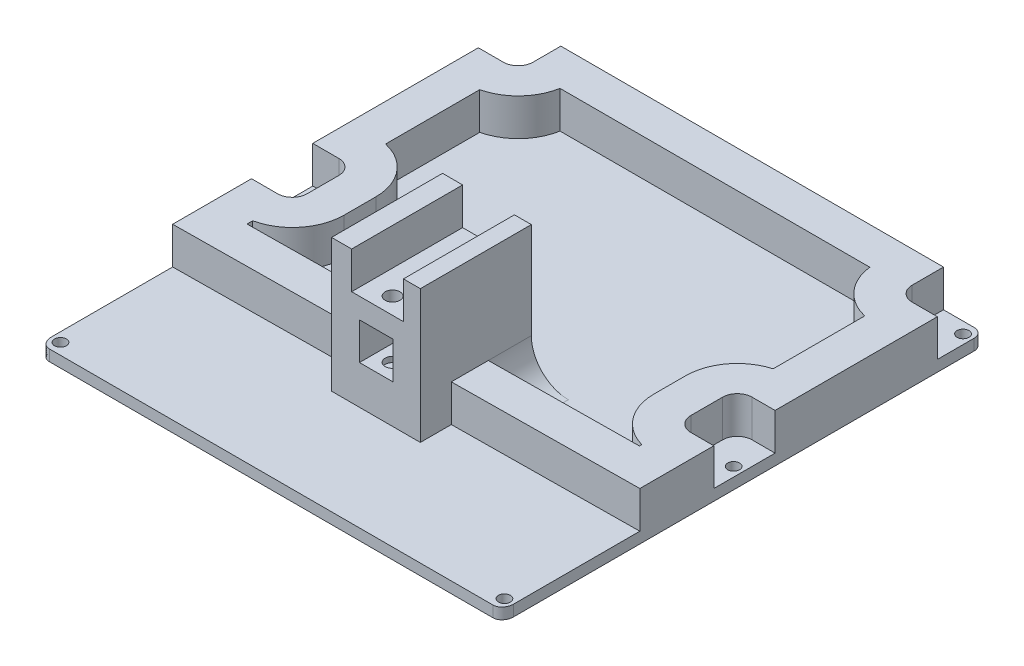
SolidWorks part; units mm, degrees
ref_plane "Front Plane" through (0, 0, 0) normal (0, 0, 1) x (1, 0, 0)
ref_plane "Top Plane" through (0, 0, 0) normal (0, 1, 0) x (1, 0, 0)
ref_plane "Right Plane" through (0, 0, 0) normal (1, 0, 0) x (0, 0, -1)
sketch "Sketch1" plane through (0, 0, 0) normal (0, 1, 0) x (-1, 0, 0)
  line L12 (60, 65) -> (-60, 65)
  line L13 (-62.5, 61.9766) -> (-62.5, -62.5)
  line L14 (-60, -65) -> (60, -65)
  line L15 (62.5, -62.5) -> (62.5, 61.9766)
  circle A3 centre (60, 61.9766) radius 1.6
  arc A6 (-62.5, -62.5) -> (-60, -65) centre (-60, -62.5) ccw
  arc A7 (60, -65) -> (62.5, -62.5) centre (60, -62.5) ccw
  circle A9 centre (-60, 61.9766) radius 1.6
  circle A11 centre (-60, 0.0234) radius 1.6
  circle A13 centre (60, 0.0234) radius 1.6
  circle A15 centre (-60, -61.9766) radius 1.6
  circle A17 centre (60, -61.9766) radius 1.6
  spline S2 degree 3 poles (-60, 65) (-60.1828, 65) (-60.3613, 64.9755) (-60.7103, 64.8812) (-60.8803, 64.8107) (-61.1953, 64.6346) (-61.3442, 64.527) (-61.614, 64.2859) (-61.7356, 64.1524) (-62.0644, 63.7166) (-62.2274, 63.3897) (-62.4459, 62.6988) (-62.5, 62.3406) (-62.5, 61.9766) knots 0 0 0 0 0.125 0.125 0.25 0.25 0.375 0.375 0.5 0.5 0.75 0.75 1 1 1 1
  spline S3 degree 3 poles (62.5, 61.9766) (62.5, 62.3418) (62.4462, 62.6962) (62.2839, 63.2118) (62.215, 63.3825) (62.0516, 63.705) (61.9573, 63.8579) (61.7414, 64.1454) (61.6183, 64.2815) (61.3473, 64.5247) (61.2009, 64.631) (60.8836, 64.8094) (60.7133, 64.8801) (60.3654, 64.9748) (60.1838, 65) (60, 65) knots 0 0 0 0 0.25 0.25 0.375 0.375 0.5 0.5 0.625 0.625 0.75 0.75 0.875 0.875 1 1 1 1
extrude "Boss-Extrude1" add sketch "Sketch1" along normal blind 3
sketch "Sketch2" plane through (0, 3, 0) normal (0, 1, 0) x (1, 0, 0)
  line L0 (-62.5, -29.1617) -> (62.5, -27.8758)
  line L1 (-62.5, 53.4681) -> (-55.7296, 53.4681)
  line L2 (-62.5, -7.8419) -> (-55.4569, -7.8419)
  line L4 (-60, -65) -> (60, -65)
  line L5 (62.5, -61.9766) -> (62.5, 62.5)
  line L6 (60, 65) -> (-60, 65)
  line L7 (-62.5, 62.5) -> (-62.5, -61.9766)
  line L9 (62.5, -27.8758) -> (62.5, -7.8748)
  line L10 (51.7018, 65) -> (-51.7296, 65)
  line L11 (-62.5, 53.4681) -> (-62.5, 8.71)
  line L12 (-62.5, 8.71) -> (-55.4569, 8.71)
  line L13 (-51.4569, -3.8419) -> (-51.4569, 4.71)
  line L16 (-51.7296, 57.4681) -> (-51.7296, 65)
  line L17 (56.2971, -7.8748) -> (62.5, -7.8748)
  line L18 (52.2971, -3.8748) -> (52.2971, 4.6771)
  line L19 (56.2971, 8.6771) -> (62.5, 8.6771)
  line L21 (55.7018, 52.5438) -> (62.5, 52.5438)
  line L22 (51.7018, 56.5438) -> (51.7018, 65)
  line L25 (62.5, 8.6771) -> (62.5, 52.5438)
  line L26 (-62.5, -7.8419) -> (-62.5, -29.1617)
  line L27 (-52.5, -19.0583) -> (52.5, -17.9781)
  line L28 (52.5, -17.9781) -> (52.5, -17.35)
  line L29 (52.5, -17.35) -> (52.5, -17.35)
  line L30 (42.2971, -3.8748) -> (42.2971, 4.6771)
  line L31 (52.5, 18.1523) -> (52.5, 18.1523)
  line L32 (52.5, 18.1523) -> (52.5, 42.9149)
  line L33 (52.5, 42.9149) -> (52.5, 42.9149)
  line L34 (41.7872, 55) -> (41.7872, 55)
  line L35 (41.7872, 55) -> (-41.9488, 55)
  line L36 (-41.9488, 55) -> (-41.9488, 55)
  line L37 (-52.5, 43.8457) -> (-52.5, 43.8457)
  line L38 (-52.5, 43.8457) -> (-52.5, 18.3941)
  line L39 (-52.5, 18.3941) -> (-52.5, 18.3941)
  line L40 (-41.4569, -3.8419) -> (-41.4569, 4.71)
  line L41 (-52.5, -17.5261) -> (-52.5, -17.5261)
  line L42 (-52.5, -17.5261) -> (-52.5, -19.0583)
  arc A2 (62.5, 62.5) -> (60, 65) centre (60, 62.5) ccw
  arc A3 (-60, 65) -> (-62.5, 62.5) centre (-60, 62.5) ccw
  arc A12 (51.7018, 56.5438) -> (55.7018, 52.5438) centre (55.7018, 56.5438) ccw
  arc A13 (52.2971, 4.6771) -> (56.2971, 8.6771) centre (56.2971, 4.6771) cw
  arc A14 (52.2971, -3.8748) -> (56.2971, -7.8748) centre (56.2971, -3.8748) ccw
  arc A15 (-51.7296, 57.4681) -> (-55.7296, 53.4681) centre (-55.7296, 57.4681) cw
  arc A16 (-55.4569, 8.71) -> (-51.4569, 4.71) centre (-55.4569, 4.71) cw
  arc A17 (-51.4569, -3.8419) -> (-55.4569, -7.8419) centre (-55.4569, -3.8419) cw
  arc A18 (42.2971, -3.8748) -> (52.5, -17.35) centre (56.2971, -3.8748) ccw
  arc A19 (42.2971, 4.6771) -> (52.5, 18.1523) centre (56.2971, 4.6771) cw
  arc A20 (41.7872, 55) -> (52.5, 42.9149) centre (55.7018, 56.5438) ccw
  arc A21 (-41.9488, 55) -> (-52.5, 43.8457) centre (-55.7296, 57.4681) cw
  arc A22 (-52.5, 18.3941) -> (-41.4569, 4.71) centre (-55.4569, 4.71) cw
  arc A23 (-41.4569, -3.8419) -> (-52.5, -17.5261) centre (-55.4569, -3.8419) cw
  spline S2 degree 3 poles (860.3992, 418.2014) (3902.2501, 922.7942) (-91.7664, 30.4633) (-62.2839, -63.2118) (-62.215, -63.3825) (-62.0516, -63.705) (-61.9573, -63.8579) (-61.7414, -64.1454) (-61.6183, -64.2815) (-61.3473, -64.5247) (-61.2009, -64.631) (-60.8836, -64.8094) (-60.7133, -64.8801) (-47.0235, -68.6046) (12.5277, 61.0266) (-2399.9231, 1807.1371) knots -67.764616 -67.764616 -67.764616 -67.764616 0.25 0.25 0.375 0.375 0.5 0.5 0.625 0.625 0.75 0.75 0.875 0.875 10.587203 10.587203 10.587203 10.587203 only from (-62.5, -61.9766) to (-60, -65)
  spline S3 degree 3 poles (-151.1581, 912.4506) (15.3217, 43.5533) (48.1013, -68.288) (60.7103, -64.8812) (60.8803, -64.8107) (61.1953, -64.6346) (61.3442, -64.527) (61.614, -64.2859) (61.7356, -64.1524) (62.0644, -63.7166) (62.2274, -63.3897) (68.3307, -44.0868) (-91.6735, 12.9984) (-248.2096, -1012.4796) knots -8.782602 -8.782602 -8.782602 -8.782602 0.125 0.125 0.25 0.25 0.375 0.375 0.5 0.5 0.75 0.75 14.46808 14.46808 14.46808 14.46808 only from (60, -65) to (62.5, -61.9766)
  spline S4 degree 3 poles (-62.5, -61.9766) (-62.5, -62.3418) (-62.4462, -62.6962) (-62.2839, -63.2118) (-62.215, -63.3825) (-62.0516, -63.705) (-61.9573, -63.8579) (-61.7414, -64.1454) (-61.6183, -64.2815) (-61.3473, -64.5247) (-61.2009, -64.631) (-60.8836, -64.8094) (-60.7133, -64.8801) (-60.3654, -64.9748) (-60.1838, -65) (-60, -65) knots 0 0 0 0 0.25 0.25 0.375 0.375 0.5 0.5 0.625 0.625 0.75 0.75 0.875 0.875 1 1 1 1
  line M13 (62.5, -61.9766) -> (62.5, 62.5)
  line M15 (60, 65) -> (-60, 65)
  line M17 (-62.5, 62.5) -> (-62.5, -61.9766)
  dimension "D2" = 4
  dimension "D3" = 10
  dimension "D1" = 0
extrude "Boss-Extrude2" add sketch "Sketch2" along normal blind 10 contours L13 A17 L2 L0 L17 A14 L18 A13 L19 L21 A12 L22 L16 A15 L1 L12 A16 M17 M13 M15
sketch "Sketch4" plane through (0, 3, 0) normal (0, 1, 0) x (1, 0, 0)
  line L1 (-11.9425, -6.7629) -> (12.0575, -6.7629)
  line L2 (-11.9425, -6.7629) -> (-11.9425, -36.7629)
  line L3 (-11.9425, -36.7629) -> (12.0575, -36.7629)
  line L4 (12.0575, -6.7629) -> (12.0575, -36.7629)
  dimension "D1" = 30
  dimension "D2" = 24
extrude "Boss-Extrude3" add sketch "Sketch4" along normal blind 36 contours L2 L1 L4 L3
sketch "Sketch5" plane through (0, 39, 0) normal (0, 1, 0) x (1, 0, 0)
  line L1 (-6.512, 3.276) -> (7.488, 3.276)
  line L2 (-6.512, 3.276) -> (-6.512, -43.6101)
  line L3 (-6.512, -43.6101) -> (7.488, -43.6101)
  line L4 (7.488, 3.276) -> (7.488, -43.6101)
  dimension "D1" = 14
extrude "Cut-Extrude1" cut sketch "Sketch5" against normal blind 10 contours L2 L1 L4 L3
fillet "Fillet1" radius 10 2 edges at (12.0575, 3, 12.5785) (-11.9425, 3, 12.702)
sketch "Sketch6" plane through (0, 29, 0) normal (0, 1, 0) x (1, 0, 0)
  line L1 (-3.9534, -14.1316) -> (3.8122, -14.1316) construction
  line L2 (-3.9534, -14.1316) -> (-3.9534, -34.1316) construction
  line L3 (-3.9534, -34.1316) -> (3.8122, -34.1316) construction
  line L4 (3.8122, -14.1316) -> (3.8122, -34.1316) construction
  circle A0 centre (0.2906, -16.0473) radius 2
  circle A1 centre (0.0306, -32.2513) radius 2
  point P6 (0.5558, -9.7189)
  point P9 (0.4856, -25.3881)
  point P10 (0.7456, -9.1841)
  dimension "D2" = 4
  dimension "D3" = 4
  dimension "D1" = 20
extrude "Cut-Extrude2" cut sketch "Sketch6" against normal blind 17
sketch "Sketch7" plane through (0, 0, 36.7629) normal (0, 0, 1) x (1, 0, 0)
  line L1 (-4.3976, 23.4784) -> (4.6024, 23.4784)
  line L2 (-4.3976, 23.4784) -> (-4.3976, 13.4784)
  line L3 (-4.3976, 13.4784) -> (4.6024, 13.4784)
  line L4 (4.6024, 23.4784) -> (4.6024, 13.4784)
  dimension "D1" = 9
  dimension "D2" = 10
extrude "Cut-Extrude3" cut sketch "Sketch7" against normal blind 43 contours L2 L1 L4 L3
